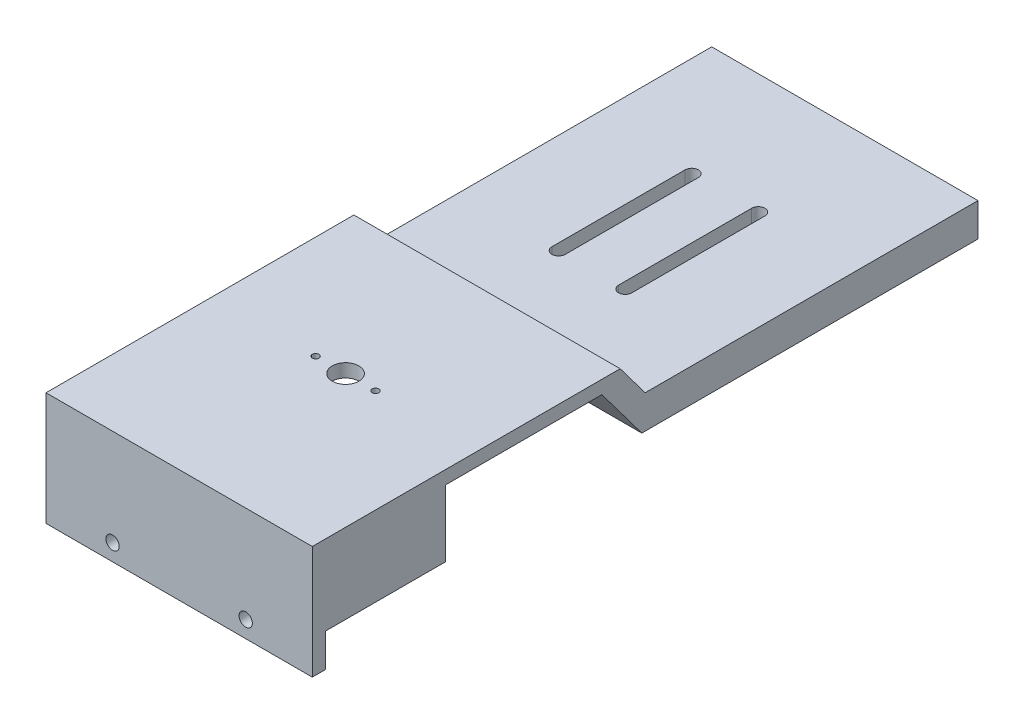
SolidWorks part; units mm, degrees
ref_plane "前视基准面" through (0, 0, 0) normal (0, 0, 1) x (1, 0, 0)
ref_plane "上视基准面" through (0, 0, 0) normal (0, 1, 0) x (1, 0, 0)
ref_plane "右视基准面" through (0, 0, 0) normal (1, 0, 0) x (0, 0, -1)
sketch "草图1" plane through (0, 0, 0) normal (0, 0, 1) x (1, 0, 0)
  line L1 (-20, 6) -> (20, 6)
  line L2 (-20, 6) -> (-20, -6)
  line L3 (-20, -6) -> (20, -6)
  line L4 (20, 6) -> (20, -6)
  line L5 (-20, 6) -> (20, -6) construction
  line L6 (-20, -6) -> (20, 6) construction
  point P0 (0, 0)
  dimension "D1" = 40
  dimension "D2" = 12
extrude "凸台-拉伸1" add sketch "草图1" along normal blind 20
sketch "草图2" plane through (0, 0, 0) normal (0, 0, -1) x (-1, 0, 0)
  line L0 (20, 6) -> (20, -6) construction
  line L1 (-20, 6) -> (20, 6)
  line L2 (-20, 6) -> (-20, 4)
  line L3 (-20, 4) -> (20, 4)
  line L4 (20, 6) -> (20, 4)
  dimension "D1" = 2
extrude "凸台-拉伸2" add sketch "草图2" along normal blind 23.5
sketch "草图3" plane through (0, -6, 0) normal (0, -1, 0) x (1, 0, 0)
  line L0 (20, 20) -> (20, 0) construction
  line L1 (-20, 20) -> (20, 20)
  line L2 (-20, 20) -> (-20, 18)
  line L3 (-20, 18) -> (20, 18)
  line L4 (20, 20) -> (20, 18)
  dimension "D1" = 2
extrude "凸台-拉伸3" add sketch "草图3" along normal blind 5
sketch "草图4" plane through (0, 6, 0) normal (0, 1, 0) x (1, 0, 0)
  line L0 (20, -20) -> (-20, -20) construction
  line L1 (0, 0) -> (0, 10.6678) construction
  line L2 (4.5, 5) -> (-4.5, 5) construction
  circle A0 centre (-4.5, 5) radius 0.5
  circle A1 centre (4.5, 5) radius 0.5
  circle A2 centre (0, 5) radius 2
  dimension "D1" = 25
  dimension "D2" = 1
  dimension "D3" = 4.5
  dimension "D4" = 4
extrude "切除-拉伸1" cut sketch "草图4" against normal up to next
sketch "草图5" plane through (0, 0, 18) normal (0, 0, -1) x (-1, 0, 0)
  line L0 (0, 0) -> (0, -19.4023) construction
  line L1 (-20, -8.5) -> (21.1287, -8.5) construction
  line L2 (-20, -11) -> (-20, -6) construction
  circle A0 centre (-10, -8.5) radius 1
  circle A1 centre (10, -8.5) radius 1
  point P9 (0, 0)
  dimension "D1" = 2
  dimension "D2" = 10
extrude "切除-拉伸2" cut sketch "草图5" against normal up to next
sketch "草图6" plane through (20, 0, 0) normal (1, 0, 0) x (0, 0, -1)
  line L0 (23.5, 4) -> (29.5, -4)
  line L1 (29.5, -4) -> (80, -4)
  line L2 (23.5, 4) -> (23.5, 6)
  line L3 (23.5, 6) -> (80, 6)
  line L4 (80, 6) -> (80, -4)
  dimension "D1" = 10
  dimension "D2" = 6
  dimension "D3" = 56.5
extrude "凸台-拉伸4" add sketch "草图6" against normal up to surface (40 mm away) up to face at (-20, -1.75, 3.625)
sketch "草图7" plane through (-20, 0, 0) normal (-1, 0, 0) x (0, 0, 1)
  line L0 (-30, 1) -> (-26.25, 6)
  line L2 (-80, 6) -> (-80, 1)
  line L3 (-80, 1) -> (-30, 1)
  line L5 (20, 6) -> (-80, 6) construction
  line L6 (-26.25, 6) -> (-80, 6)
  line L7 (-29.5, -4) -> (-23.5, 4) construction
  dimension "D1" = 5
  dimension "D2" = 50
extrude "切除-拉伸3" cut sketch "草图7" against normal up to surface (40 mm away) up to face at (20, -2.2, -13.7)
sketch "草图9" plane through (0, 1, 0) normal (0, 1, 0) x (1, 0, 0)
  line L0 (-5, 62) -> (-5, 42) construction
  line L1 (-4, 62) -> (-4, 42)
  line L2 (-6, 62) -> (-6, 42)
  line L3 (0, 80) -> (0, 34.484) construction
  line L4 (20, 80) -> (-20, 80) construction
  line L5 (5, 62) -> (5, 42) construction
  line L6 (4, 62) -> (4, 42)
  line L7 (6, 62) -> (6, 42)
  arc A0 (-4, 62) -> (-6, 62) centre (-5, 62) ccw
  arc A1 (-6, 42) -> (-4, 42) centre (-5, 42) ccw
  arc A2 (4, 62) -> (6, 62) centre (5, 62) cw
  arc A3 (6, 42) -> (4, 42) centre (5, 42) cw
  point P2 (-5, 52)
  point P14 (5, 52)
  dimension "D1" = 1
  dimension "D2" = 5
  dimension "D3" = 18
  dimension "D4" = 20
extrude "切除-拉伸5" cut sketch "草图9" against normal up to next
